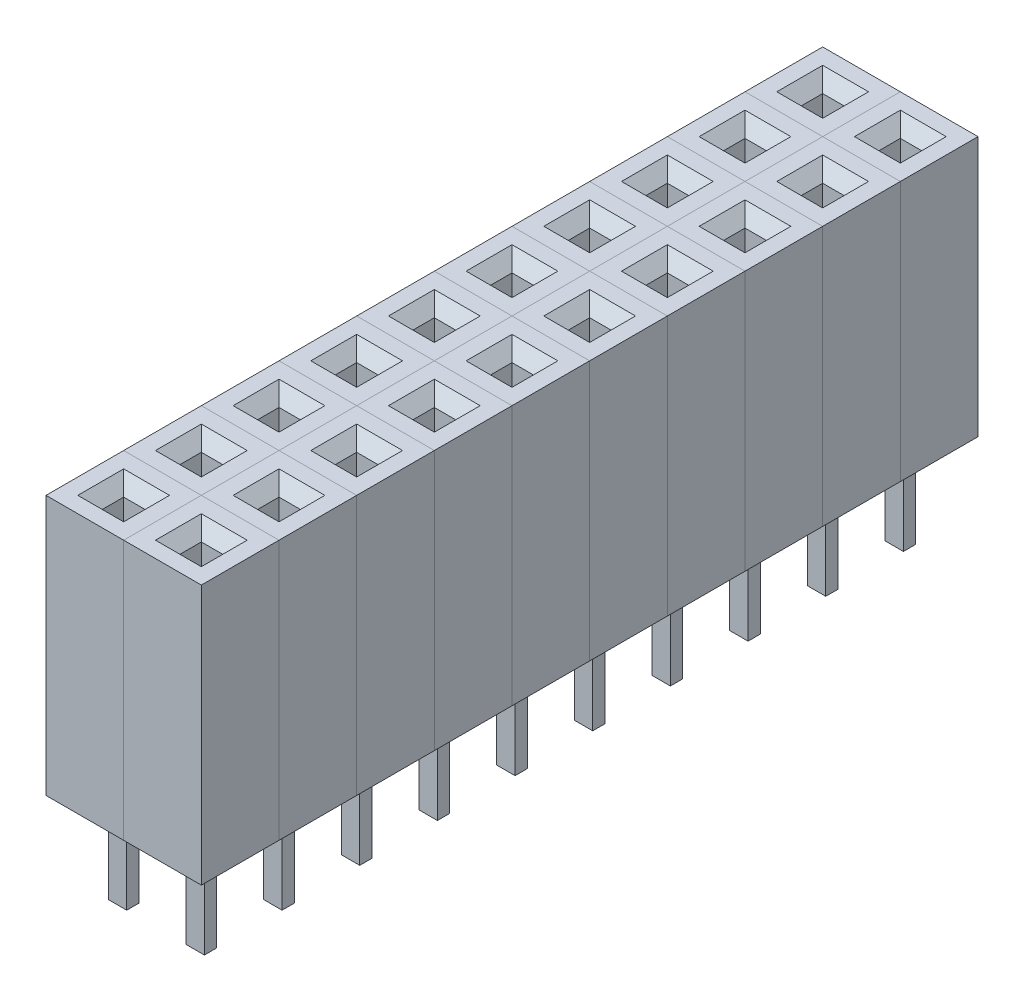
SolidWorks part; units mm, degrees
ref_plane "Спереди" through (0, 0, 0) normal (0, 0, 1) x (1, 0, 0)
ref_plane "Сверху" through (0, 0, 0) normal (0, 1, 0) x (1, 0, 0)
ref_plane "Справа" through (0, 0, 0) normal (1, 0, 0) x (0, 0, -1)
sketch "Эскиз1" plane through (0, 0, 0) normal (0, 1, 0) x (1, 0, 0)
  line L1 (1.27, 1.27) -> (-1.27, 1.27)
  line L2 (1.27, 1.27) -> (1.27, -1.27)
  line L3 (1.27, -1.27) -> (-1.27, -1.27)
  line L4 (-1.27, 1.27) -> (-1.27, -1.27)
  line L5 (1.27, 1.27) -> (-1.27, -1.27) construction
  line L6 (1.27, -1.27) -> (-1.27, 1.27) construction
  point P0 (0, 0)
  dimension "D1" = 2.54
  dimension "D2" = 2.54
extrude "Бобышка-Вытянуть1" add sketch "Эскиз1" along normal blind 8.5
sketch "Эскиз2" plane through (0, 8.5, 0) normal (0, 1, 0) x (1, 0, 0)
  line L1 (0.35, 0.35) -> (-0.35, 0.35)
  line L2 (0.35, 0.35) -> (0.35, -0.35)
  line L3 (0.35, -0.35) -> (-0.35, -0.35)
  line L4 (-0.35, 0.35) -> (-0.35, -0.35)
  line L5 (0.35, 0.35) -> (-0.35, -0.35) construction
  line L6 (0.35, -0.35) -> (-0.35, 0.35) construction
  point P0 (0, 0)
  dimension "D1" = 0.7
  dimension "D2" = 0.7
extrude "Вырез-Вытянуть1" cut sketch "Эскиз2" along normal through all and the other way blind 8
chamfer "Фаска1" distance 0.4 angle 45 4 edges at (0.35, 8.5, 0) (0, 8.5, -0.35) (-0.35, 8.5, 0) (0, 8.5, 0.35)
sketch "Эскиз3" plane through (0, 0, 0) normal (0, -1, 0) x (1, 0, 0)
  line L1 (0.3, 0.2) -> (-0.3, 0.2)
  line L2 (0.3, 0.2) -> (0.3, -0.2)
  line L3 (0.3, -0.2) -> (-0.3, -0.2)
  line L4 (-0.3, 0.2) -> (-0.3, -0.2)
  line L5 (0.3, 0.2) -> (-0.3, -0.2) construction
  line L6 (0.3, -0.2) -> (-0.3, 0.2) construction
  point P0 (0, 0)
  dimension "D1" = 0.6
  dimension "D2" = 0.4
extrude "Бобышка-Вытянуть2" add sketch "Эскиз3" along normal blind 3
chamfer "Фаска2" [suppressed] distance 0.2 angle 45
pattern_linear "Линейный массив1" count 2 spacing 2.54 along (1, 0, 0) of bodies 105
pattern_linear "LPattern1" count 10 spacing 2.54 along (0, 0, -1) of bodies 106 105
ref_plane "MidPlane" through (0, 0, -11.43) normal (0, 0, 1) x (1, 0, 0)
